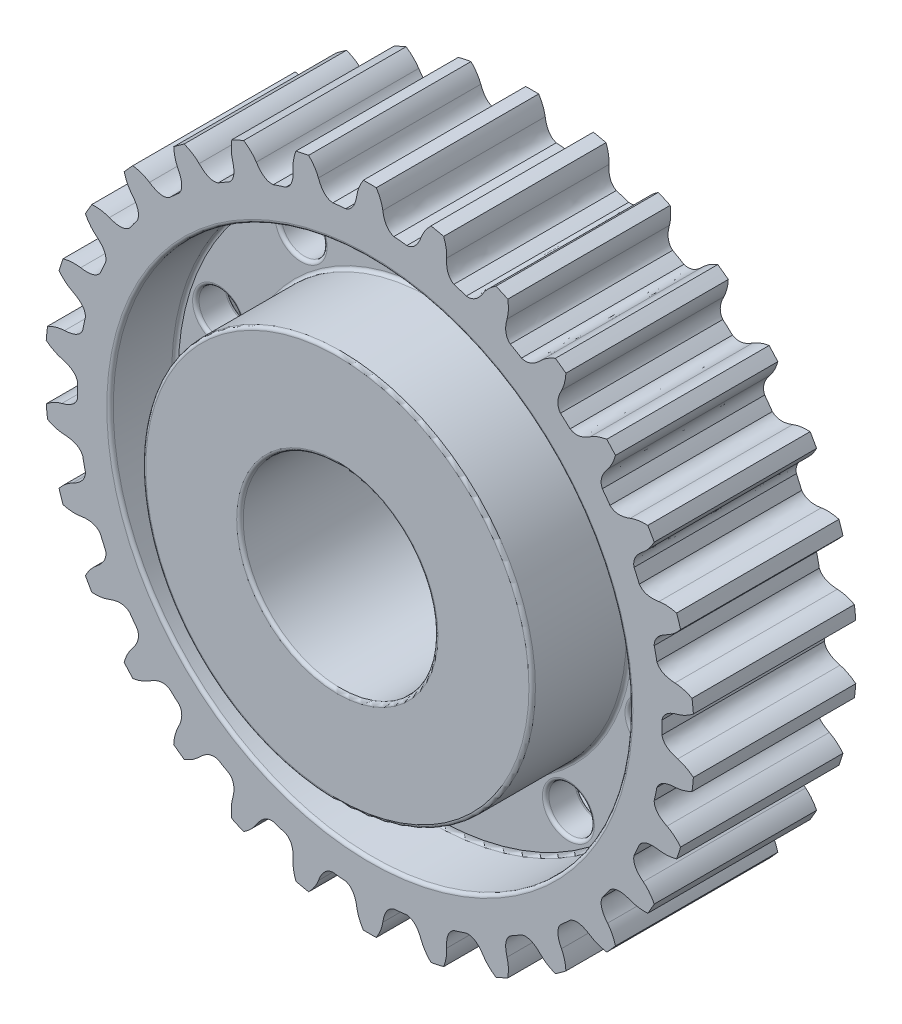
SolidWorks part; units mm, degrees
ref_plane "Front Plane" through (0, 0, 0) normal (0, 0, 1) x (1, 0, 0)
ref_plane "Top Plane" through (0, 0, 0) normal (0, 1, 0) x (1, 0, 0)
ref_plane "Right Plane" through (0, 0, 0) normal (1, 0, 0) x (0, 0, -1)
sketch "Sketch1" plane through (0, 0, 0) normal (0, 0, 1) x (1, 0, 0)
  line L0 (0, 0) -> (0, 50)
  line L1 (-1.8942, 44.9472) -> (-1.8943, 44.9493)
  line L3 (1.8942, 44.9472) -> (1.8943, 44.9493)
  arc A0 (0.9999, 49.99) -> (-0.9999, 49.99) centre (0, 0) ccw
  arc A1 (4.7024, 44.7407) -> (3.7067, 44.8341) centre (0, 0) ccw
  arc A3 (-4.7024, 44.7407) -> (-3.7067, 44.8341) centre (0, 0) cw
  arc A4 (4.7024, 44.7407) -> (5.6958, 44.6251) centre (0, 0) cw
  arc A5 (11.3716, 48.6897) -> (9.4154, 49.1055) centre (0, 0) ccw
  arc A6 (13.9018, 42.7853) -> (12.9473, 43.0837) centre (0, 0) ccw
  arc A7 (13.9018, 42.7853) -> (14.8494, 42.4657) centre (0, 0) cw
  arc A8 (21.2463, 45.2614) -> (19.4193, 46.0749) centre (0, 0) ccw
  arc A9 (22.4936, 38.96) -> (21.622, 39.4504) centre (0, 0) ccw
  arc A10 (22.4936, 38.96) -> (23.354, 38.4504) centre (0, 0) cw
  arc A11 (30.1924, 39.855) -> (28.5744, 41.0305) centre (0, 0) ccw
  arc A12 (30.1023, 33.4319) -> (29.3517, 34.0928) centre (0, 0) ccw
  arc A13 (30.1023, 33.4319) -> (30.838, 32.7545) centre (0, 0) cw
  arc A14 (37.8189, 32.7067) -> (36.4807, 34.1929) centre (0, 0) ccw
  arc A15 (36.3953, 26.4428) -> (35.7986, 27.2452) centre (0, 0) ccw
  arc A16 (36.3953, 26.4428) -> (36.9741, 25.6272) centre (0, 0) cw
  arc A17 (43.7926, 24.129) -> (42.7926, 25.861) centre (0, 0) ccw
  arc A18 (41.0978, 18.2979) -> (40.6809, 19.2069) centre (0, 0) ccw
  arc A19 (41.0978, 18.2979) -> (41.4944, 17.3798) centre (0, 0) cw
  arc A20 (47.8523, 14.4968) -> (47.2343, 16.3988) centre (0, 0) ccw
  arc A21 (44.004, 9.3533) -> (43.7853, 10.3292) centre (0, 0) ccw
  arc A22 (44.004, 9.3533) -> (44.2011, 8.3729) centre (0, 0) cw
  arc A23 (49.8207, 4.2309) -> (49.6116, 6.2199) centre (0, 0) ccw
  arc A24 (44.9871, 0) -> (44.976, 1) centre (0, 0) ccw
  arc A25 (44.9871, 0) -> (44.976, -1) centre (0, 0) cw
  arc A26 (49.6116, -6.2199) -> (49.8207, -4.2309) centre (0, 0) ccw
  arc A27 (44.004, -9.3533) -> (44.2011, -8.3729) centre (0, 0) ccw
  arc A28 (44.004, -9.3533) -> (43.7853, -10.3292) centre (0, 0) cw
  arc A29 (47.2343, -16.3988) -> (47.8523, -14.4968) centre (0, 0) ccw
  arc A30 (41.0978, -18.2979) -> (41.4944, -17.3798) centre (0, 0) ccw
  arc A31 (41.0978, -18.2979) -> (40.6809, -19.2069) centre (0, 0) cw
  arc A32 (42.7926, -25.861) -> (43.7926, -24.129) centre (0, 0) ccw
  arc A33 (36.3953, -26.4428) -> (36.9741, -25.6272) centre (0, 0) ccw
  arc A34 (36.3953, -26.4428) -> (35.7986, -27.2452) centre (0, 0) cw
  arc A35 (36.4807, -34.1929) -> (37.8189, -32.7067) centre (0, 0) ccw
  arc A36 (30.1023, -33.4319) -> (30.838, -32.7545) centre (0, 0) ccw
  arc A37 (30.1023, -33.4319) -> (29.3517, -34.0928) centre (0, 0) cw
  arc A38 (28.5744, -41.0305) -> (30.1924, -39.855) centre (0, 0) ccw
  arc A39 (22.4936, -38.96) -> (23.354, -38.4504) centre (0, 0) ccw
  arc A40 (22.4936, -38.96) -> (21.622, -39.4504) centre (0, 0) cw
  arc A41 (19.4193, -46.0749) -> (21.2463, -45.2614) centre (0, 0) ccw
  arc A42 (13.9018, -42.7853) -> (14.8494, -42.4657) centre (0, 0) ccw
  arc A43 (13.9018, -42.7853) -> (12.9473, -43.0837) centre (0, 0) cw
  arc A44 (9.4154, -49.1055) -> (11.3716, -48.6897) centre (0, 0) ccw
  arc A45 (4.7024, -44.7407) -> (5.6958, -44.6251) centre (0, 0) ccw
  arc A46 (4.7024, -44.7407) -> (3.7067, -44.8341) centre (0, 0) cw
  arc A47 (-0.9999, -49.99) -> (0.9999, -49.99) centre (0, 0) ccw
  arc A48 (-4.7024, -44.7407) -> (-3.7067, -44.8341) centre (0, 0) ccw
  arc A49 (-4.7024, -44.7407) -> (-5.6958, -44.6251) centre (0, 0) cw
  arc A50 (-11.3716, -48.6897) -> (-9.4154, -49.1055) centre (0, 0) ccw
  arc A51 (-13.9018, -42.7853) -> (-12.9473, -43.0837) centre (0, 0) ccw
  arc A52 (-13.9018, -42.7853) -> (-14.8494, -42.4657) centre (0, 0) cw
  arc A53 (-21.2463, -45.2614) -> (-19.4193, -46.0749) centre (0, 0) ccw
  arc A54 (-22.4936, -38.96) -> (-21.622, -39.4504) centre (0, 0) ccw
  arc A55 (-22.4936, -38.96) -> (-23.354, -38.4504) centre (0, 0) cw
  arc A56 (-30.1924, -39.855) -> (-28.5744, -41.0305) centre (0, 0) ccw
  arc A57 (-30.1023, -33.4319) -> (-29.3517, -34.0928) centre (0, 0) ccw
  arc A58 (-30.1023, -33.4319) -> (-30.838, -32.7545) centre (0, 0) cw
  arc A59 (-37.8189, -32.7067) -> (-36.4807, -34.1929) centre (0, 0) ccw
  arc A60 (-36.3953, -26.4428) -> (-35.7986, -27.2452) centre (0, 0) ccw
  arc A61 (-36.3953, -26.4428) -> (-36.9741, -25.6272) centre (0, 0) cw
  arc A62 (-43.7926, -24.129) -> (-42.7926, -25.861) centre (0, 0) ccw
  arc A63 (-41.0978, -18.2979) -> (-40.6809, -19.2069) centre (0, 0) ccw
  arc A64 (-41.0978, -18.2979) -> (-41.4944, -17.3798) centre (0, 0) cw
  arc A65 (-47.8523, -14.4968) -> (-47.2343, -16.3988) centre (0, 0) ccw
  arc A66 (-44.004, -9.3533) -> (-43.7853, -10.3292) centre (0, 0) ccw
  arc A67 (-44.004, -9.3533) -> (-44.2011, -8.3729) centre (0, 0) cw
  arc A68 (-49.8207, -4.2309) -> (-49.6116, -6.2199) centre (0, 0) ccw
  arc A69 (-44.9871, 0) -> (-44.976, -1) centre (0, 0) ccw
  arc A70 (-44.9871, 0) -> (-44.976, 1) centre (0, 0) cw
  arc A71 (-49.6116, 6.2199) -> (-49.8207, 4.2309) centre (0, 0) ccw
  arc A72 (-44.004, 9.3533) -> (-44.2011, 8.3729) centre (0, 0) ccw
  arc A73 (-44.004, 9.3533) -> (-43.7853, 10.3292) centre (0, 0) cw
  arc A74 (-47.2343, 16.3988) -> (-47.8523, 14.4968) centre (0, 0) ccw
  arc A75 (-41.0978, 18.2979) -> (-41.4944, 17.3798) centre (0, 0) ccw
  arc A76 (-41.0978, 18.2979) -> (-40.6809, 19.2069) centre (0, 0) cw
  arc A77 (-42.7926, 25.861) -> (-43.7926, 24.129) centre (0, 0) ccw
  arc A78 (-36.3953, 26.4428) -> (-36.9741, 25.6272) centre (0, 0) ccw
  arc A79 (-36.3953, 26.4428) -> (-35.7986, 27.2452) centre (0, 0) cw
  arc A80 (-36.4807, 34.1929) -> (-37.8189, 32.7067) centre (0, 0) ccw
  arc A81 (-30.1023, 33.4319) -> (-30.838, 32.7545) centre (0, 0) ccw
  arc A82 (-30.1023, 33.4319) -> (-29.3517, 34.0928) centre (0, 0) cw
  arc A83 (-28.5744, 41.0305) -> (-30.1924, 39.855) centre (0, 0) ccw
  arc A84 (-22.4936, 38.96) -> (-23.354, 38.4504) centre (0, 0) ccw
  arc A85 (-22.4936, 38.96) -> (-21.622, 39.4504) centre (0, 0) cw
  arc A86 (-19.4193, 46.0749) -> (-21.2463, 45.2614) centre (0, 0) ccw
  arc A87 (-13.9018, 42.7853) -> (-14.8494, 42.4657) centre (0, 0) ccw
  arc A88 (-13.9018, 42.7853) -> (-12.9473, 43.0837) centre (0, 0) cw
  arc A89 (-9.4154, 49.1055) -> (-11.3716, 48.6897) centre (0, 0) ccw
  arc A90 (-4.7024, 44.7407) -> (-5.6958, 44.6251) centre (0, 0) ccw
  circle A91 centre (0, 0) radius 15
  spline S0 degree 3 poles (0.9999, 49.99) (1.5446, 49.1506) (1.8825, 48.2763) (2.0136, 47.3672) knots 0 0 0 0 0.538133 0.538133 0.538133 0.538133
  spline S1 degree 2 poles (2, 47.4569) (2.3196, 45.2626) (3.7067, 44.8341) knots 0 0 0 0.757811 0.757811 0.757811
  spline S2 degree 2 poles (-2, 47.4569) (-2.3196, 45.2626) (-3.7067, 44.8341) knots 0 0 0 0.757811 0.757811 0.757811
  spline S3 degree 3 poles (-0.9999, 49.99) (-1.5446, 49.1506) (-1.8825, 48.2763) (-2.0136, 47.3672) knots 0 0 0 0 0.538133 0.538133 0.538133 0.538133
  spline S4 degree 2 poles (7.9106, 46.8357) (7.1417, 44.7557) (5.6958, 44.6251) knots 0 0 0 0.757811 0.757811 0.757811
  spline S5 degree 3 poles (9.4154, 49.1055) (8.7081, 48.3976) (8.1958, 47.6127) (7.8786, 46.7507) knots 0 0 0 0 0.538133 0.538133 0.538133 0.538133
  spline S6 degree 3 poles (11.3716, 48.6897) (11.7298, 47.7554) (11.8786, 46.8299) (11.8178, 45.9134) knots 0 0 0 0 0.538133 0.538133 0.538133 0.538133
  spline S7 degree 2 poles (11.8231, 46.004) (11.6795, 43.7912) (12.9473, 43.0837) knots 0 0 0 0.757811 0.757811 0.757811
  spline S8 degree 2 poles (17.4754, 44.1675) (16.2909, 42.2929) (14.8494, 42.4657) knots 0 0 0 0.757811 0.757811 0.757811
  spline S9 degree 3 poles (19.4193, 46.0749) (18.5803, 45.5295) (17.916, 44.8683) (17.4264, 44.0911) knots 0 0 0 0 0.538133 0.538133 0.538133 0.538133
  spline S10 degree 3 poles (21.2463, 45.2614) (21.4024, 44.273) (21.3555, 43.3369) (21.1055, 42.453) knots 0 0 0 0 0.538133 0.538133 0.538133 0.538133
  spline S11 degree 2 poles (21.1296, 42.5406) (20.529, 40.4059) (21.622, 39.4504) knots 0 0 0 0.757811 0.757811 0.757811
  spline S12 degree 2 poles (26.2764, 39.569) (24.7281, 37.9816) (23.354, 38.4504) knots 0 0 0 0.757811 0.757811 0.757811
  spline S13 degree 3 poles (28.5744, 41.0305) (27.6404, 40.6715) (26.8531, 40.1628) (26.2127, 39.5044) knots 0 0 0 0 0.538133 0.538133 0.538133 0.538133
  spline S14 degree 3 poles (30.1924, 39.855) (30.1396, 38.8557) (29.8991, 37.9498) (29.4708, 37.1373) knots 0 0 0 0 0.538133 0.538133 0.538133 0.538133
  spline S15 degree 2 poles (29.5125, 37.2179) (28.4813, 35.2548) (29.3517, 34.0928) knots 0 0 0 0.757811 0.757811 0.757811
  spline S16 degree 2 poles (33.9291, 33.2412) (32.0845, 32.0104) (30.838, 32.7545) knots 0 0 0 0.757811 0.757811 0.757811
  spline S17 degree 3 poles (36.4807, 34.1929) (35.4924, 34.036) (34.6166, 33.7021) (33.8533, 33.1912) knots 0 0 0 0 0.538133 0.538133 0.538133 0.538133
  spline S18 degree 3 poles (37.8189, 32.7067) (37.5595, 31.7403) (37.1359, 30.9042) (36.548, 30.1984) knots 0 0 0 0 0.538133 0.538133 0.538133 0.538133
  spline S19 degree 2 poles (36.6056, 30.2686) (35.1887, 28.5628) (35.7986, 27.2452) knots 0 0 0 0.757811 0.757811 0.757811
  spline S20 degree 2 poles (40.0989, 25.4605) (38.0387, 24.6401) (36.9741, 25.6272) knots 0 0 0 0.757811 0.757811 0.757811
  spline S21 degree 3 poles (42.7926, 25.861) (41.7933, 25.913) (40.8672, 25.7684) (40.0143, 25.4274) knots 0 0 0 0 0.538133 0.538133 0.538133 0.538133
  spline S22 degree 3 poles (43.7926, 24.129) (43.3379, 23.2376) (42.7497, 22.5078) (42.028, 21.9397) knots 0 0 0 0 0.538133 0.538133 0.538133 0.538133
  spline S23 degree 2 poles (42.0989, 21.9964) (40.3583, 20.6225) (40.6809, 19.2069) knots 0 0 0 0.757811 0.757811 0.757811
  spline S24 degree 2 poles (44.5162, 16.5671) (42.3305, 16.193) (41.4944, 17.3798) knots 0 0 0 0.757811 0.757811 0.757811
  spline S25 degree 3 poles (47.2343, 16.3988) (46.2677, 16.6574) (45.3317, 16.7086) (44.4266, 16.5523) knots 0 0 0 0 0.538133 0.538133 0.538133 0.538133
  spline S26 degree 3 poles (47.8523, 14.4968) (47.2223, 13.7193) (46.4952, 13.1278) (45.6711, 12.7222) knots 0 0 0 0 0.538133 0.538133 0.538133 0.538133
  spline S27 degree 2 poles (45.7522, 12.7629) (43.7641, 11.7808) (43.7853, 10.3292) knots 0 0 0 0.757811 0.757811 0.757811
  spline S28 degree 2 poles (46.9879, 6.9496) (44.7721, 7.0381) (44.2011, 8.3729) knots 0 0 0 0.757811 0.757811 0.757811
  spline S29 degree 3 poles (49.6116, 6.2199) (48.7199, 6.6738) (47.815, 6.9184) (46.8972, 6.9538) knots 0 0 0 0 0.538133 0.538133 0.538133 0.538133
  spline S30 degree 3 poles (49.8207, 4.2309) (49.0428, 3.6015) (48.2086, 3.174) (47.3182, 2.9486) knots 0 0 0 0 0.538133 0.538133 0.538133 0.538133
  spline S31 degree 2 poles (47.406, 2.9716) (45.2571, 2.4243) (44.976, 1) knots 0 0 0 0.757811 0.757811 0.757811
  spline S32 degree 2 poles (47.406, -2.9716) (45.2571, -2.4243) (44.976, -1) knots 0 0 0 0.757811 0.757811 0.757811
  spline S33 degree 3 poles (49.8207, -4.2309) (49.0428, -3.6015) (48.2086, -3.174) (47.3182, -2.9486) knots 0 0 0 0 0.538133 0.538133 0.538133 0.538133
  spline S34 degree 3 poles (49.6116, -6.2199) (48.7199, -6.6738) (47.815, -6.9184) (46.8972, -6.9538) knots 0 0 0 0 0.538133 0.538133 0.538133 0.538133
  spline S35 degree 2 poles (46.9879, -6.9496) (44.7721, -7.0381) (44.2011, -8.3729) knots 0 0 0 0.757811 0.757811 0.757811
  spline S36 degree 2 poles (45.7522, -12.7629) (43.7641, -11.7808) (43.7853, -10.3292) knots 0 0 0 0.757811 0.757811 0.757811
  spline S37 degree 3 poles (47.8523, -14.4968) (47.2223, -13.7193) (46.4952, -13.1278) (45.6711, -12.7222) knots 0 0 0 0 0.538133 0.538133 0.538133 0.538133
  spline S38 degree 3 poles (47.2343, -16.3988) (46.2677, -16.6574) (45.3317, -16.7086) (44.4266, -16.5523) knots 0 0 0 0 0.538133 0.538133 0.538133 0.538133
  spline S39 degree 2 poles (44.5162, -16.5671) (42.3305, -16.193) (41.4944, -17.3798) knots 0 0 0 0.757811 0.757811 0.757811
  spline S40 degree 2 poles (42.0989, -21.9964) (40.3583, -20.6225) (40.6809, -19.2069) knots 0 0 0 0.757811 0.757811 0.757811
  spline S41 degree 3 poles (43.7926, -24.129) (43.3379, -23.2376) (42.7497, -22.5078) (42.028, -21.9397) knots 0 0 0 0 0.538133 0.538133 0.538133 0.538133
  spline S42 degree 3 poles (42.7926, -25.861) (41.7933, -25.913) (40.8672, -25.7684) (40.0143, -25.4274) knots 0 0 0 0 0.538133 0.538133 0.538133 0.538133
  spline S43 degree 2 poles (40.0989, -25.4605) (38.0387, -24.6401) (36.9741, -25.6272) knots 0 0 0 0.757811 0.757811 0.757811
  spline S44 degree 2 poles (36.6056, -30.2686) (35.1887, -28.5628) (35.7986, -27.2452) knots 0 0 0 0.757811 0.757811 0.757811
  spline S45 degree 3 poles (37.8189, -32.7067) (37.5595, -31.7403) (37.1359, -30.9042) (36.548, -30.1984) knots 0 0 0 0 0.538133 0.538133 0.538133 0.538133
  spline S46 degree 3 poles (36.4807, -34.1929) (35.4924, -34.036) (34.6166, -33.7021) (33.8533, -33.1912) knots 0 0 0 0 0.538133 0.538133 0.538133 0.538133
  spline S47 degree 2 poles (33.9291, -33.2412) (32.0845, -32.0104) (30.838, -32.7545) knots 0 0 0 0.757811 0.757811 0.757811
  spline S48 degree 2 poles (29.5125, -37.2179) (28.4813, -35.2548) (29.3517, -34.0928) knots 0 0 0 0.757811 0.757811 0.757811
  spline S49 degree 3 poles (30.1924, -39.855) (30.1396, -38.8557) (29.8991, -37.9498) (29.4708, -37.1373) knots 0 0 0 0 0.538133 0.538133 0.538133 0.538133
  spline S50 degree 3 poles (28.5744, -41.0305) (27.6404, -40.6715) (26.8531, -40.1628) (26.2127, -39.5044) knots 0 0 0 0 0.538133 0.538133 0.538133 0.538133
  spline S51 degree 2 poles (26.2764, -39.569) (24.7281, -37.9816) (23.354, -38.4504) knots 0 0 0 0.757811 0.757811 0.757811
  spline S52 degree 2 poles (21.1296, -42.5406) (20.529, -40.4059) (21.622, -39.4504) knots 0 0 0 0.757811 0.757811 0.757811
  spline S53 degree 3 poles (21.2463, -45.2614) (21.4024, -44.273) (21.3555, -43.3369) (21.1055, -42.453) knots 0 0 0 0 0.538133 0.538133 0.538133 0.538133
  spline S54 degree 3 poles (19.4193, -46.0749) (18.5803, -45.5295) (17.916, -44.8683) (17.4264, -44.0911) knots 0 0 0 0 0.538133 0.538133 0.538133 0.538133
  spline S55 degree 2 poles (17.4754, -44.1675) (16.2909, -42.2929) (14.8494, -42.4657) knots 0 0 0 0.757811 0.757811 0.757811
  spline S56 degree 2 poles (11.8231, -46.004) (11.6795, -43.7912) (12.9473, -43.0837) knots 0 0 0 0.757811 0.757811 0.757811
  spline S57 degree 3 poles (11.3716, -48.6897) (11.7298, -47.7554) (11.8786, -46.8299) (11.8178, -45.9134) knots 0 0 0 0 0.538133 0.538133 0.538133 0.538133
  spline S58 degree 3 poles (9.4154, -49.1055) (8.7081, -48.3976) (8.1958, -47.6127) (7.8786, -46.7507) knots 0 0 0 0 0.538133 0.538133 0.538133 0.538133
  spline S59 degree 2 poles (7.9106, -46.8357) (7.1417, -44.7557) (5.6958, -44.6251) knots 0 0 0 0.757811 0.757811 0.757811
  spline S60 degree 2 poles (2, -47.4569) (2.3196, -45.2626) (3.7067, -44.8341) knots 0 0 0 0.757811 0.757811 0.757811
  spline S61 degree 3 poles (0.9999, -49.99) (1.5446, -49.1506) (1.8825, -48.2763) (2.0136, -47.3672) knots 0 0 0 0 0.538133 0.538133 0.538133 0.538133
  spline S62 degree 3 poles (-0.9999, -49.99) (-1.5446, -49.1506) (-1.8825, -48.2763) (-2.0136, -47.3672) knots 0 0 0 0 0.538133 0.538133 0.538133 0.538133
  spline S63 degree 2 poles (-2, -47.4569) (-2.3196, -45.2626) (-3.7067, -44.8341) knots 0 0 0 0.757811 0.757811 0.757811
  spline S64 degree 2 poles (-7.9106, -46.8357) (-7.1417, -44.7557) (-5.6958, -44.6251) knots 0 0 0 0.757811 0.757811 0.757811
  spline S65 degree 3 poles (-9.4154, -49.1055) (-8.7081, -48.3976) (-8.1958, -47.6127) (-7.8786, -46.7507) knots 0 0 0 0 0.538133 0.538133 0.538133 0.538133
  spline S66 degree 3 poles (-11.3716, -48.6897) (-11.7298, -47.7554) (-11.8786, -46.8299) (-11.8178, -45.9134) knots 0 0 0 0 0.538133 0.538133 0.538133 0.538133
  spline S67 degree 2 poles (-11.8231, -46.004) (-11.6795, -43.7912) (-12.9473, -43.0837) knots 0 0 0 0.757811 0.757811 0.757811
  spline S68 degree 2 poles (-17.4754, -44.1675) (-16.2909, -42.2929) (-14.8494, -42.4657) knots 0 0 0 0.757811 0.757811 0.757811
  spline S69 degree 3 poles (-19.4193, -46.0749) (-18.5803, -45.5295) (-17.916, -44.8683) (-17.4264, -44.0911) knots 0 0 0 0 0.538133 0.538133 0.538133 0.538133
  spline S70 degree 3 poles (-21.2463, -45.2614) (-21.4024, -44.273) (-21.3555, -43.3369) (-21.1055, -42.453) knots 0 0 0 0 0.538133 0.538133 0.538133 0.538133
  spline S71 degree 2 poles (-21.1296, -42.5406) (-20.529, -40.4059) (-21.622, -39.4504) knots 0 0 0 0.757811 0.757811 0.757811
  spline S72 degree 2 poles (-26.2764, -39.569) (-24.7281, -37.9816) (-23.354, -38.4504) knots 0 0 0 0.757811 0.757811 0.757811
  spline S73 degree 3 poles (-28.5744, -41.0305) (-27.6404, -40.6715) (-26.8531, -40.1628) (-26.2127, -39.5044) knots 0 0 0 0 0.538133 0.538133 0.538133 0.538133
  spline S74 degree 3 poles (-30.1924, -39.855) (-30.1396, -38.8557) (-29.8991, -37.9498) (-29.4708, -37.1373) knots 0 0 0 0 0.538133 0.538133 0.538133 0.538133
  spline S75 degree 2 poles (-29.5125, -37.2179) (-28.4813, -35.2548) (-29.3517, -34.0928) knots 0 0 0 0.757811 0.757811 0.757811
  spline S76 degree 2 poles (-33.9291, -33.2412) (-32.0845, -32.0104) (-30.838, -32.7545) knots 0 0 0 0.757811 0.757811 0.757811
  spline S77 degree 3 poles (-36.4807, -34.1929) (-35.4924, -34.036) (-34.6166, -33.7021) (-33.8533, -33.1912) knots 0 0 0 0 0.538133 0.538133 0.538133 0.538133
  spline S78 degree 3 poles (-37.8189, -32.7067) (-37.5595, -31.7403) (-37.1359, -30.9042) (-36.548, -30.1984) knots 0 0 0 0 0.538133 0.538133 0.538133 0.538133
  spline S79 degree 2 poles (-36.6056, -30.2686) (-35.1887, -28.5628) (-35.7986, -27.2452) knots 0 0 0 0.757811 0.757811 0.757811
  spline S80 degree 2 poles (-40.0989, -25.4605) (-38.0387, -24.6401) (-36.9741, -25.6272) knots 0 0 0 0.757811 0.757811 0.757811
  spline S81 degree 3 poles (-42.7926, -25.861) (-41.7933, -25.913) (-40.8672, -25.7684) (-40.0143, -25.4274) knots 0 0 0 0 0.538133 0.538133 0.538133 0.538133
  spline S82 degree 3 poles (-43.7926, -24.129) (-43.3379, -23.2376) (-42.7497, -22.5078) (-42.028, -21.9397) knots 0 0 0 0 0.538133 0.538133 0.538133 0.538133
  spline S83 degree 2 poles (-42.0989, -21.9964) (-40.3583, -20.6225) (-40.6809, -19.2069) knots 0 0 0 0.757811 0.757811 0.757811
  spline S84 degree 2 poles (-44.5162, -16.5671) (-42.3305, -16.193) (-41.4944, -17.3798) knots 0 0 0 0.757811 0.757811 0.757811
  spline S85 degree 3 poles (-47.2343, -16.3988) (-46.2677, -16.6574) (-45.3317, -16.7086) (-44.4266, -16.5523) knots 0 0 0 0 0.538133 0.538133 0.538133 0.538133
  spline S86 degree 3 poles (-47.8523, -14.4968) (-47.2223, -13.7193) (-46.4952, -13.1278) (-45.6711, -12.7222) knots 0 0 0 0 0.538133 0.538133 0.538133 0.538133
  spline S87 degree 2 poles (-45.7522, -12.7629) (-43.7641, -11.7808) (-43.7853, -10.3292) knots 0 0 0 0.757811 0.757811 0.757811
  spline S88 degree 2 poles (-46.9879, -6.9496) (-44.7721, -7.0381) (-44.2011, -8.3729) knots 0 0 0 0.757811 0.757811 0.757811
  spline S89 degree 3 poles (-49.6116, -6.2199) (-48.7199, -6.6738) (-47.815, -6.9184) (-46.8972, -6.9538) knots 0 0 0 0 0.538133 0.538133 0.538133 0.538133
  spline S90 degree 3 poles (-49.8207, -4.2309) (-49.0428, -3.6015) (-48.2086, -3.174) (-47.3182, -2.9486) knots 0 0 0 0 0.538133 0.538133 0.538133 0.538133
  spline S91 degree 2 poles (-47.406, -2.9716) (-45.2571, -2.4243) (-44.976, -1) knots 0 0 0 0.757811 0.757811 0.757811
  spline S92 degree 2 poles (-47.406, 2.9716) (-45.2571, 2.4243) (-44.976, 1) knots 0 0 0 0.757811 0.757811 0.757811
  spline S93 degree 3 poles (-49.8207, 4.2309) (-49.0428, 3.6015) (-48.2086, 3.174) (-47.3182, 2.9486) knots 0 0 0 0 0.538133 0.538133 0.538133 0.538133
  spline S94 degree 3 poles (-49.6116, 6.2199) (-48.7199, 6.6738) (-47.815, 6.9184) (-46.8972, 6.9538) knots 0 0 0 0 0.538133 0.538133 0.538133 0.538133
  spline S95 degree 2 poles (-46.9879, 6.9496) (-44.7721, 7.0381) (-44.2011, 8.3729) knots 0 0 0 0.757811 0.757811 0.757811
  spline S96 degree 2 poles (-45.7522, 12.7629) (-43.7641, 11.7808) (-43.7853, 10.3292) knots 0 0 0 0.757811 0.757811 0.757811
  spline S97 degree 3 poles (-47.8523, 14.4968) (-47.2223, 13.7193) (-46.4952, 13.1278) (-45.6711, 12.7222) knots 0 0 0 0 0.538133 0.538133 0.538133 0.538133
  spline S98 degree 3 poles (-47.2343, 16.3988) (-46.2677, 16.6574) (-45.3317, 16.7086) (-44.4266, 16.5523) knots 0 0 0 0 0.538133 0.538133 0.538133 0.538133
  spline S99 degree 2 poles (-44.5162, 16.5671) (-42.3305, 16.193) (-41.4944, 17.3798) knots 0 0 0 0.757811 0.757811 0.757811
  spline S100 degree 2 poles (-42.0989, 21.9964) (-40.3583, 20.6225) (-40.6809, 19.2069) knots 0 0 0 0.757811 0.757811 0.757811
  spline S101 degree 3 poles (-43.7926, 24.129) (-43.3379, 23.2376) (-42.7497, 22.5078) (-42.028, 21.9397) knots 0 0 0 0 0.538133 0.538133 0.538133 0.538133
  spline S102 degree 3 poles (-42.7926, 25.861) (-41.7933, 25.913) (-40.8672, 25.7684) (-40.0143, 25.4274) knots 0 0 0 0 0.538133 0.538133 0.538133 0.538133
  spline S103 degree 2 poles (-40.0989, 25.4605) (-38.0387, 24.6401) (-36.9741, 25.6272) knots 0 0 0 0.757811 0.757811 0.757811
  spline S104 degree 2 poles (-36.6056, 30.2686) (-35.1887, 28.5628) (-35.7986, 27.2452) knots 0 0 0 0.757811 0.757811 0.757811
  spline S105 degree 3 poles (-37.8189, 32.7067) (-37.5595, 31.7403) (-37.1359, 30.9042) (-36.548, 30.1984) knots 0 0 0 0 0.538133 0.538133 0.538133 0.538133
  spline S106 degree 3 poles (-36.4807, 34.1929) (-35.4924, 34.036) (-34.6166, 33.7021) (-33.8533, 33.1912) knots 0 0 0 0 0.538133 0.538133 0.538133 0.538133
  spline S107 degree 2 poles (-33.9291, 33.2412) (-32.0845, 32.0104) (-30.838, 32.7545) knots 0 0 0 0.757811 0.757811 0.757811
  spline S108 degree 2 poles (-29.5125, 37.2179) (-28.4813, 35.2548) (-29.3517, 34.0928) knots 0 0 0 0.757811 0.757811 0.757811
  spline S109 degree 3 poles (-30.1924, 39.855) (-30.1396, 38.8557) (-29.8991, 37.9498) (-29.4708, 37.1373) knots 0 0 0 0 0.538133 0.538133 0.538133 0.538133
  spline S110 degree 3 poles (-28.5744, 41.0305) (-27.6404, 40.6715) (-26.8531, 40.1628) (-26.2127, 39.5044) knots 0 0 0 0 0.538133 0.538133 0.538133 0.538133
  spline S111 degree 2 poles (-26.2764, 39.569) (-24.7281, 37.9816) (-23.354, 38.4504) knots 0 0 0 0.757811 0.757811 0.757811
  spline S112 degree 2 poles (-21.1296, 42.5406) (-20.529, 40.4059) (-21.622, 39.4504) knots 0 0 0 0.757811 0.757811 0.757811
  spline S113 degree 3 poles (-21.2463, 45.2614) (-21.4024, 44.273) (-21.3555, 43.3369) (-21.1055, 42.453) knots 0 0 0 0 0.538133 0.538133 0.538133 0.538133
  spline S114 degree 3 poles (-19.4193, 46.0749) (-18.5803, 45.5295) (-17.916, 44.8683) (-17.4264, 44.0911) knots 0 0 0 0 0.538133 0.538133 0.538133 0.538133
  spline S115 degree 2 poles (-17.4754, 44.1675) (-16.2909, 42.2929) (-14.8494, 42.4657) knots 0 0 0 0.757811 0.757811 0.757811
  spline S116 degree 2 poles (-11.8231, 46.004) (-11.6795, 43.7912) (-12.9473, 43.0837) knots 0 0 0 0.757811 0.757811 0.757811
  spline S117 degree 3 poles (-11.3716, 48.6897) (-11.7298, 47.7554) (-11.8786, 46.8299) (-11.8178, 45.9134) knots 0 0 0 0 0.538133 0.538133 0.538133 0.538133
  spline S118 degree 3 poles (-9.4154, 49.1055) (-8.7081, 48.3976) (-8.1958, 47.6127) (-7.8786, 46.7507) knots 0 0 0 0 0.538133 0.538133 0.538133 0.538133
  spline S119 degree 2 poles (-7.9106, 46.8357) (-7.1417, 44.7557) (-5.6958, 44.6251) knots 0 0 0 0.757811 0.757811 0.757811
  point P369 (0, 0)
  dimension "D1" = 30
extrude "Boss-Extrude1" add sketch "Sketch1" along normal mid plane 12.5 contours S119 S118 A89 S117 S116 A88 A87 S115 S114 A86 S113 S112 A85 A84 S111 S110 A83 S109 S108 A82 A81 S107 S106 A80 S105 S104 A79 A78 S103 S102 A77 S101 S100 A76 A75 S99 S98 A74 S97 S96
sketch "Sketch2" plane through (0, 0, 6.25) normal (0, 0, 1) x (1, 0, 0)
  circle A0 centre (0, 0) radius 15
  circle A1 centre (0, 0) radius 30
extrude "Boss-Extrude2" add sketch "Sketch2" along normal blind 5
sketch "Sketch3" plane through (0, 0, 6.25) normal (0, 0, 1) x (1, 0, 0)
  circle A0 centre (0, 0) radius 30
  circle A1 centre (0, 0) radius 40
extrude "Cut-Extrude1" cut sketch "Sketch3" against normal blind 10
sketch "Sketch4" plane through (0, 0, -3.75) normal (0, 0, 1) x (1, 0, 0)
  circle A0 centre (0, 35) radius 3.5
  circle A1 centre (20.5725, 28.3156) radius 3.5
  circle A2 centre (33.287, 10.8156) radius 3.5
  circle A3 centre (33.287, -10.8156) radius 3.5
  circle A4 centre (20.5725, -28.3156) radius 3.5
  circle A5 centre (0, -35) radius 3.5
  circle A6 centre (-20.5725, -28.3156) radius 3.5
  circle A7 centre (-33.287, -10.8156) radius 3.5
  circle A8 centre (-33.287, 10.8156) radius 3.5
  circle A9 centre (-20.5725, 28.3156) radius 3.5
  point P23 (0, 0)
  dimension "D1" = 35
  dimension "D2" = 10
extrude "Cut-Extrude2" cut sketch "Sketch4" against normal up to next
fillet "Fillet1" radius 0.5 15 edges at (40, 0, -3.75) (40, 0, 6.25) (15, 0, 11.25) (30, 0, 11.25) (30, 0, -3.75) (-29.787, 10.8156, -3.75) (-29.787, -10.8156, -3.75) (-17.0725, -28.3156, -3.75) (3.5, -35, -3.75) (24.0725, -28.3156, -3.75) (36.787, -10.8156, -3.75) (36.787, 10.8156, -3.75) (24.0725, 28.3156, -3.75) (3.5, 35, -3.75) (-17.0725, 28.3156, -3.75)
mirror "Mirror1" about plane through (0, 0, -6.25) normal (0, 0, 1)
